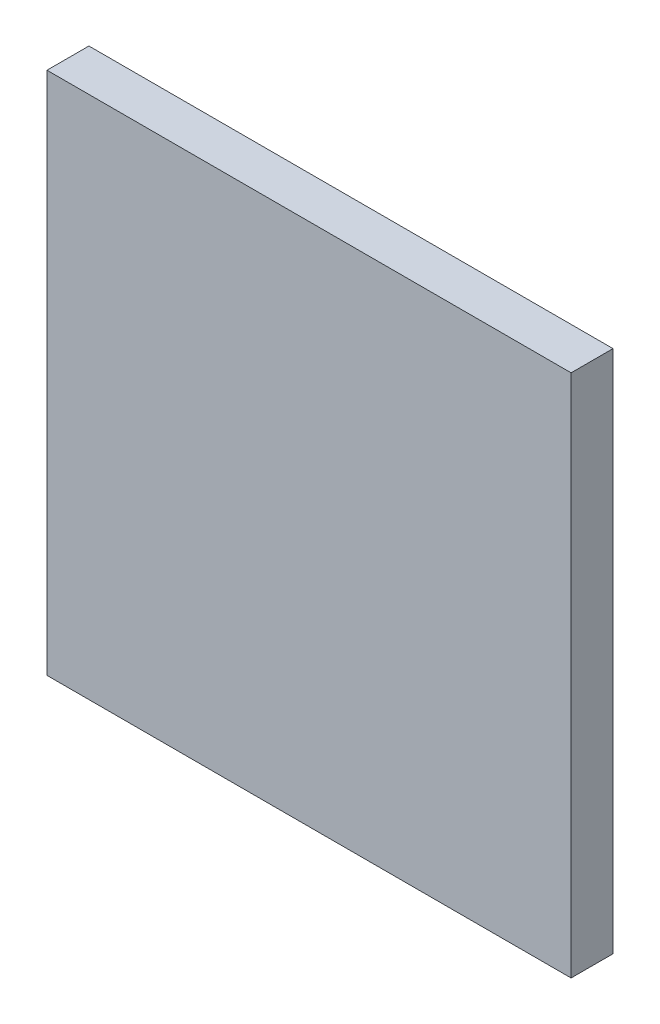
SolidWorks part; units mm, degrees
ref_plane "前视基准面" through (0, 0, 0) normal (0, 0, 1) x (1, 0, 0)
ref_plane "上视基准面" through (0, 0, 0) normal (0, 1, 0) x (1, 0, 0)
ref_plane "右视基准面" through (0, 0, 0) normal (1, 0, 0) x (0, 0, -1)
sketch "草图1" plane through (0, 0, 0) normal (0, 0, 1) x (1, 0, 0)
  line L0 (203.0052, 77.2932) -> (238.3226, 77.2932) construction
  line L1 (220.8088, 94.6175) -> (220.8088, 60.0622) construction
  line L2 (208.3088, 77.2932) -> (208.3088, 89.7932)
  line L3 (208.3088, 89.7932) -> (233.3088, 89.7932)
  line L4 (233.3088, 89.7932) -> (233.3088, 64.7932)
  line L5 (233.3088, 64.7932) -> (208.3088, 64.7932)
  line L6 (208.3088, 64.7932) -> (208.3088, 77.2932)
extrude "凸台-拉伸1" add sketch "草图1" along normal blind 2
